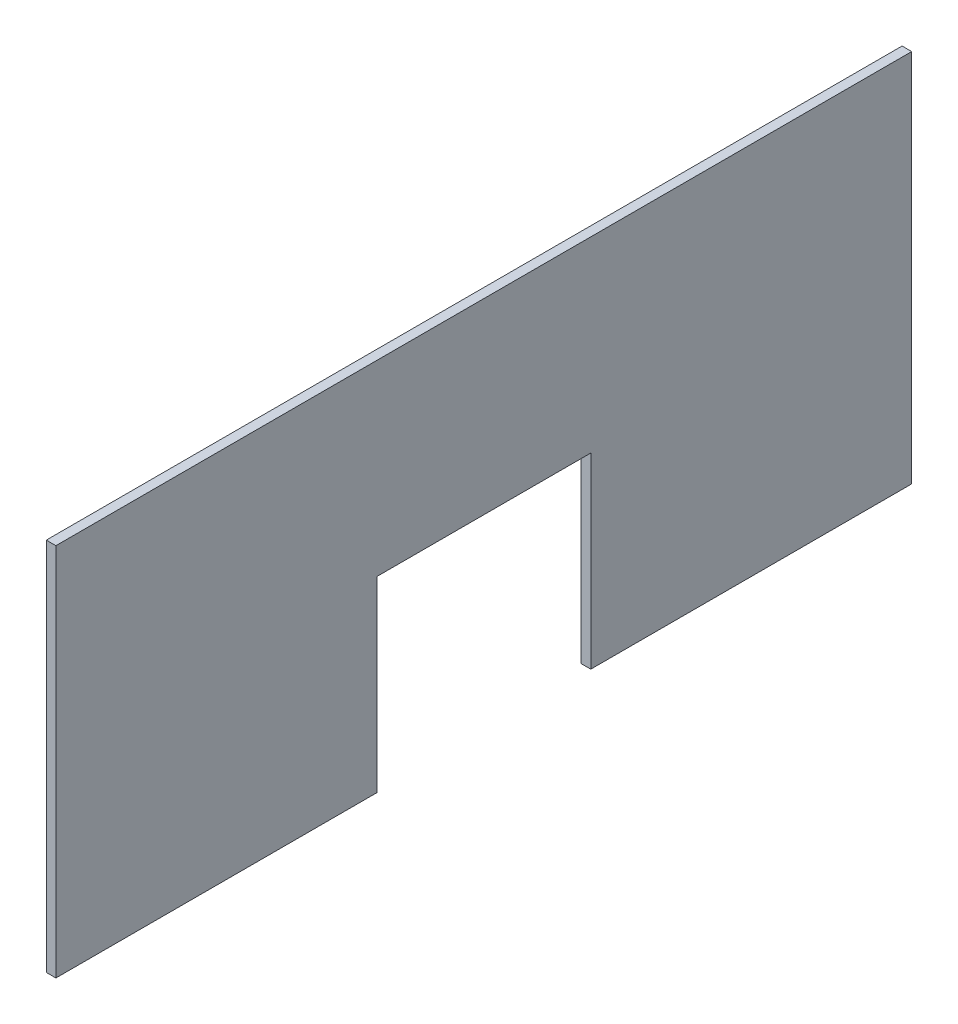
SolidWorks part; units mm, degrees
ref_plane "Спереди" through (0, 0, 0) normal (0, 0, 1) x (1, 0, 0)
ref_plane "Сверху" through (0, 0, 0) normal (0, 1, 0) x (1, 0, 0)
ref_plane "Справа" through (0, 0, 0) normal (1, 0, 0) x (0, 0, -1)
sketch "Эскиз1" plane through (0, 0, 0) normal (1, 0, 0) x (0, 0, -1)
  line L0 (32.6818, 1580.3951) -> (32.6818, 880.3951)
  line L1 (32.6818, 880.3951) -> (632.6818, 880.3951)
  line L2 (632.6818, 880.3951) -> (632.6818, 1230.3951)
  line L3 (632.6818, 1230.3951) -> (1032.6818, 1230.3951)
  line L4 (1032.6818, 1230.3951) -> (1032.6818, 880.3951)
  line L5 (1032.6818, 880.3951) -> (1632.6818, 880.3951)
  line L6 (1632.6818, 880.3951) -> (1632.6818, 1580.3951)
  line L7 (1632.6818, 1580.3951) -> (32.6818, 1580.3951)
  dimension "D1" = 1600
  dimension "D2" = 700
  dimension "D3" = 600
  dimension "D4" = 600
  dimension "D5" = 350
extrude "Бобышка-Вытянуть1" add sketch "Эскиз1" along normal blind 18
